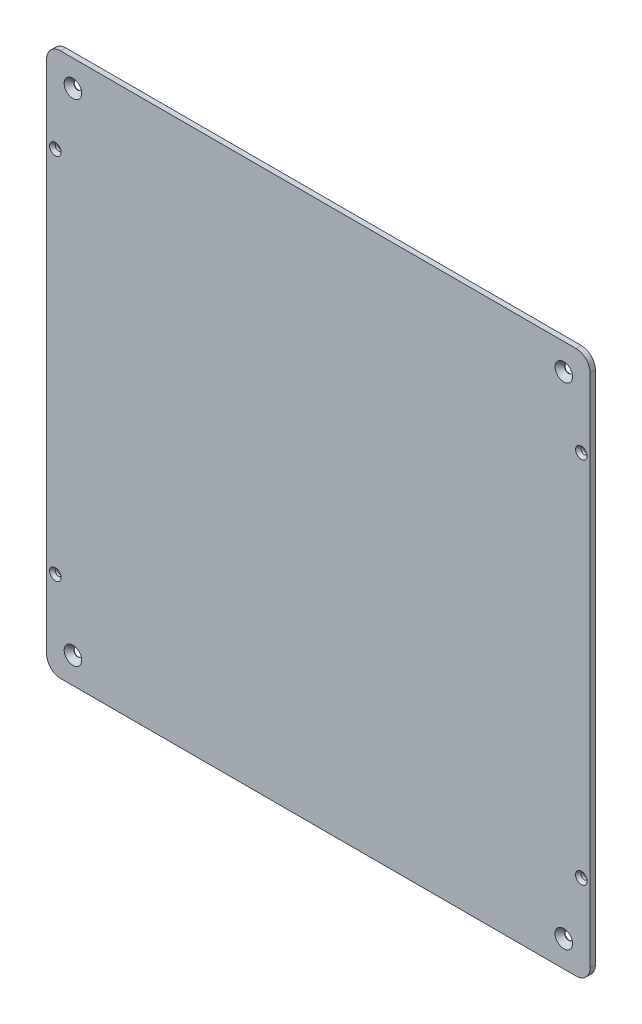
SolidWorks part; units mm, degrees
material "6061 合金"
ref_plane "前视基准面" through (0, 0, 0) normal (0, 0, 1) x (1, 0, 0)
ref_plane "上视基准面" through (0, 0, 0) normal (0, 1, 0) x (1, 0, 0)
ref_plane "右视基准面" through (0, 0, 0) normal (1, 0, 0) x (0, 0, -1)
sketch "草图1" plane through (0, 0, 0) normal (0, 0, 1) x (1, 0, 0)
  line L0 (0, 0) -> (166856.3255, 0) construction
  line L1 (0, 0) -> (0, 166856.3255) construction
  line L3 (-147, 155) -> (147, 155)
  line L4 (-155, 147) -> (-155, -147)
  line L5 (-147, -155) -> (147, -155)
  line L6 (155, 147) -> (155, -147)
  line L7 (100, 100) -> (-100, 100) construction
  line L8 (100, 100) -> (100, -100) construction
  line L9 (100, -100) -> (-100, -100) construction
  line L10 (-100, 100) -> (-100, -100) construction
  line L11 (100, 100) -> (-100, -100) construction
  line L12 (100, -100) -> (-100, 100) construction
  arc A0 (147, -155) -> (155, -147) centre (147, -147) ccw
  arc A1 (-155, -147) -> (-147, -155) centre (-147, -147) ccw
  arc A2 (147, 155) -> (155, 147) centre (147, 147) cw
  arc A3 (-147, 155) -> (-155, 147) centre (-147, 147) ccw
  point P13 (-155, -155)
  point P18 (-155, 155)
  point P19 (0, 0)
  dimension "D2" = 8
  dimension "D1" = 310
  dimension "D3" = 200
  dimension "D4" = 200
extrude "凸台-拉伸1" add sketch "草图1" along normal blind 3
hole_wizard "打孔尺寸(%根据十字)槽半沉头木螺钉的类型1" positions "草图3" profile "草图2" countersink size "M4" standard "GB" end condition through all
sketch "草图3" plane through (0, 0, 3) normal (0, 0, 1) x (1, 0, 0)
  line L0 (0, 331.6208) -> (0, -343.6074) construction
  line L3 (-325.3075, 0) -> (270.4694, 0) construction
  point P0 (-140, 140)
  point P7 (140, 140)
  point P8 (140, -140)
  point P9 (-140, -140)
  dimension "D1" = 140
  dimension "D2" = 140
sketch "草图2" plane through (-140, 140, 3) normal (1, 0, 0) x (0, -1, 0)
  line L0 (0, 0) -> (0, 3)
  line L1 (0, 3) -> (2.25, 3)
  line L2 (2.25, 3) -> (2.25, 2.75)
  line L3 (2.25, 2.75) -> (5, 0)
  line L5 (5, 0) -> (0, 0)
  line L6 (-2.25, 2.75) -> (-5, 0) construction
  line L11 (0, -6.35) -> (0, 107.95) construction
  dimension "通孔孔直径" = 4.5
  dimension "通孔孔深度" = 3
  dimension "近端锥形沉头孔直径" = 10
  dimension "近端锥形沉头孔角度" = 90
sketch "草图4" plane through (0, 0, 0) normal (0, 0, -1) x (-1, 0, 0)
  line L0 (-15, 119) -> (-15, 104)
  line L1 (-15, 104) -> (-23, 104)
  line L2 (-23, 104) -> (-23, 119)
  line L3 (-23, 119) -> (-15, 119)
  line L4 (-29, 119) -> (-29, 104)
  line L5 (-29, 104) -> (-37, 104)
  line L6 (-37, 104) -> (-37, 119)
  line L7 (-37, 119) -> (-29, 119)
  line L9 (-147, 155) -> (147, 155) construction
  line L11 (155, 147) -> (155, -147) construction
  point P12 (-37, 111.5)
  dimension "D1" = 8
  dimension "D2" = 15
  dimension "D3" = 36
  dimension "D4" = 170
  dimension "D5" = 6
  dimension "D6" = 0
  dimension "D7" = 0
  dimension "D8" = 8
extrude "凸台-拉伸2" add sketch "草图4" along normal blind 1
hole_wizard "打孔尺寸(%根据十字)槽沉头木螺钉的类型1" positions "草图5" profile "草图6" countersink size "M3" standard "GB" end condition through all
sketch "草图5" plane through (0, 0, 3) normal (0, 0, 1) x (1, 0, 0)
  line L0 (155, -147) -> (155, 147) construction
  line L1 (-147, -155) -> (147, -155) construction
  line L2 (-155, 147) -> (-155, -147) construction
  line L3 (147, 155) -> (-147, 155) construction
  point P0 (150, -105)
  point P2 (150, 105)
  point P4 (-150, 105)
  point P6 (-150, -105)
  dimension "D1" = 5
  dimension "D2" = 50
  dimension "D3" = 5
  dimension "D4" = 50
sketch "草图6" plane through (150, -105, 3) normal (1, 0, 0) x (0, -1, 0)
  line L0 (0, 0) -> (0, 4)
  line L1 (0, 4) -> (1.7, 4)
  line L2 (1.7, 4) -> (1.7, 1.6)
  line L3 (1.7, 1.6) -> (3.3, 0)
  line L5 (3.3, 0) -> (0, 0)
  line L6 (-1.7, 1.6) -> (-3.3, 0) construction
  line L11 (0, -6.35) -> (0, 107.95) construction
  dimension "通孔孔直径" = 3.4
  dimension "通孔孔深度" = 4
  dimension "近端锥形沉头孔直径" = 6.6
  dimension "近端锥形沉头孔角度" = 90
